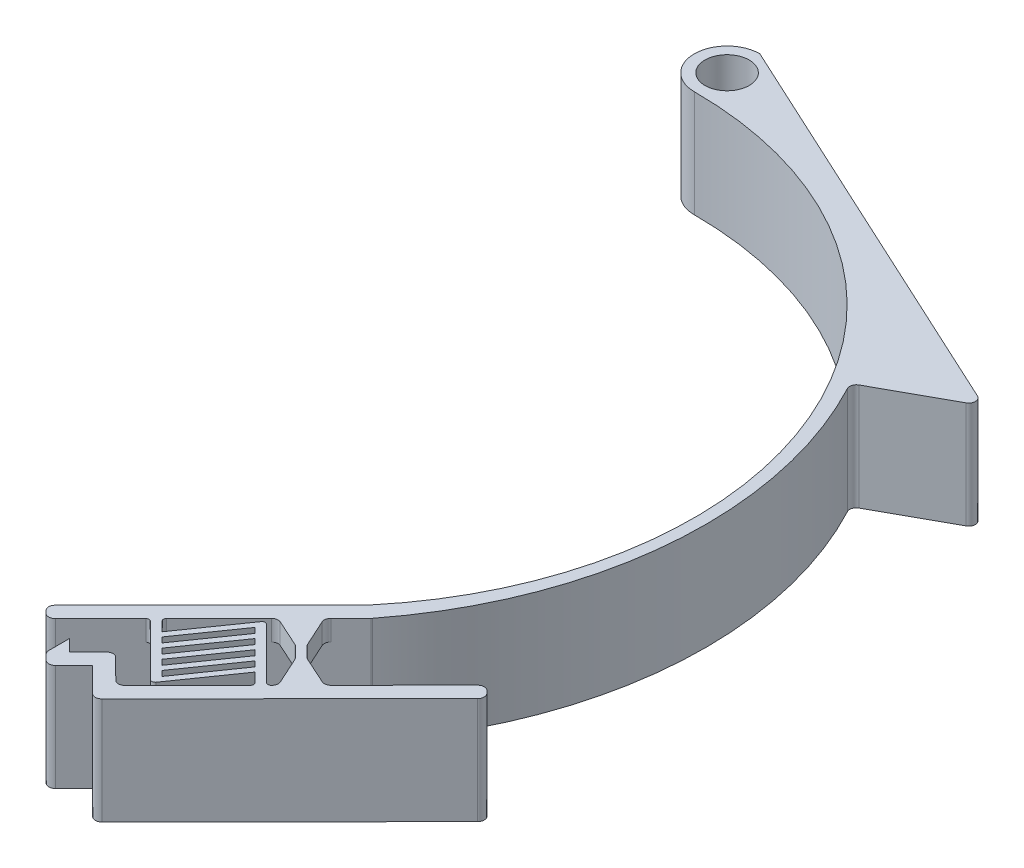
SolidWorks part; units mm, degrees
ref_plane "Front Plane" through (0, 0, 0) normal (0, 0, 1) x (1, 0, 0)
ref_plane "Top Plane" through (0, 0, 0) normal (0, 1, 0) x (1, 0, 0)
ref_plane "Right Plane" through (0, 0, 0) normal (1, 0, 0) x (0, 0, -1)
sketch "Sketch1" plane through (0, 0, 0) normal (0, 1, 0) x (1, 0, 0)
  line L0 (0, 0) -> (34.472, -28.9254) construction
  line L1 (0, 0) -> (0, -45) construction
  line L2 (0, 0) -> (63.5762, -53.3468) construction
  line L3 (0, 53) -> (50.8207, 29.4786)
  line L4 (50.8207, 29.4786) -> (40.3111, 23.6864)
  line L5 (0, 53) -> (0, 49)
  line L7 (0, 49) -> (0, 53)
  line L8 (34.472, -28.9254) -> (20.3504, -43.088)
  line L9 (20.3504, -43.088) -> (21.7666, -44.5002)
  line L10 (21.7666, -44.5002) -> (35.8883, -30.3376)
  line L11 (35.8883, -30.3376) -> (34.472, -28.9254)
  line L12 (30.2642, -52.9732) -> (28.8479, -51.561)
  line L13 (28.8479, -51.561) -> (50.0304, -30.3171)
  line L14 (50.0304, -30.3171) -> (51.4466, -31.7293)
  line L15 (51.4466, -31.7293) -> (30.2642, -52.9732)
  line L17 (22.4727, -43.7921) -> (29.2708, -50.5705)
  line L18 (36.6148, -43.7716) -> (29.8168, -36.9932)
  line L19 (29.8168, -36.9932) -> (24.5858, -44.4869)
  line L20 (24.5858, -44.4869) -> (23.1788, -43.084)
  line L21 (29.2708, -50.5705) -> (34.5017, -43.0768)
  line L22 (22.4727, -43.7921) -> (23.1788, -43.084)
  line L23 (35.9087, -44.4797) -> (34.5017, -43.0768)
  line L24 (23.1788, -43.084) -> (30.2601, -50.1448) construction
  line L25 (35.9087, -44.4797) -> (28.8274, -37.4189) construction
  line L26 (29.3086, -49.196) -> (33.9584, -42.535)
  line L27 (33.9584, -42.535) -> (33.321, -41.8995)
  line L28 (33.321, -41.8995) -> (28.6713, -48.5606)
  line L29 (28.6713, -48.5606) -> (29.3086, -49.196)
  line L30 (28.1279, -48.0187) -> (27.4906, -47.3833)
  line L31 (27.4906, -47.3833) -> (32.1403, -40.7222)
  line L32 (32.1403, -40.7222) -> (32.7777, -41.3577)
  line L33 (32.7777, -41.3577) -> (28.1279, -48.0187)
  line L34 (26.9472, -46.8415) -> (26.3099, -46.206)
  line L35 (26.3099, -46.206) -> (30.9596, -39.5449)
  line L36 (30.9596, -39.5449) -> (31.597, -40.1804)
  line L37 (31.597, -40.1804) -> (26.9472, -46.8415)
  line L38 (25.7665, -45.6642) -> (25.1292, -45.0287)
  line L39 (25.1292, -45.0287) -> (29.7789, -38.3677)
  line L40 (29.7789, -38.3677) -> (30.4163, -39.0031)
  line L41 (30.4163, -39.0031) -> (25.7665, -45.6642)
  line L42 (35.9087, -44.4797) -> (36.6148, -43.7716)
  line L43 (24.5858, -44.4869) -> (25.1292, -45.0287) construction
  line L44 (25.7665, -45.6642) -> (26.3099, -46.206) construction
  line L45 (26.9472, -46.8415) -> (27.4906, -47.3833) construction
  line L46 (28.1279, -48.0187) -> (28.6713, -48.5606) construction
  line L47 (29.3086, -49.196) -> (29.852, -49.7378) construction
  line L48 (30.2396, -36.0026) -> (34.1313, -37.7648)
  line L49 (34.1313, -37.7648) -> (35.5475, -39.1769)
  line L50 (35.5475, -39.1769) -> (37.3209, -43.0635)
  line L51 (37.3209, -43.0635) -> (40.1452, -40.2309)
  line L52 (40.1452, -40.2309) -> (36.2536, -38.4688)
  line L53 (36.2536, -38.4688) -> (34.8373, -37.0566)
  line L54 (34.8373, -37.0566) -> (33.0639, -33.1701)
  line L55 (33.0639, -33.1701) -> (30.2396, -36.0026)
  line L56 (36.0041, -30.211) -> (35.8883, -30.3376)
  line L57 (20.3504, -43.088) -> (21.7666, -44.5002)
  line L58 (20.3504, -43.088) -> (14.7017, -48.7531)
  line L59 (21.7666, -44.5002) -> (16.118, -50.1653)
  line L60 (14.7017, -48.7531) -> (16.118, -50.1653)
  line L61 (16.118, -50.1653) -> (20.3545, -45.9165) construction
  line L62 (16.118, -50.1653) -> (19.6586, -53.6957) construction
  line L63 (20.3545, -45.9165) -> (23.8951, -49.4469) construction
  line L64 (19.6586, -53.6957) -> (23.8951, -49.4469) construction
  line L69 (30.2642, -52.9732) -> (27.4399, -55.8057)
  line L70 (27.4399, -55.8057) -> (23.8992, -52.2753)
  line L71 (28.8479, -51.561) -> (30.2642, -52.9732)
  line L72 (23.8992, -52.2753) -> (21.0749, -55.1078)
  line L73 (21.0749, -55.1078) -> (19.6586, -53.6957)
  line L74 (19.6586, -53.6957) -> (23.8951, -49.4469)
  line L75 (23.8951, -49.4469) -> (27.4358, -52.9773)
  line L76 (27.4358, -52.9773) -> (28.8479, -51.561)
  line L77 (28.8479, -51.561) -> (30.2642, -52.9732)
  line L82 (19.6586, -53.6957) -> (21.0708, -52.2794)
  line L83 (21.0708, -52.2794) -> (19.6545, -50.8672)
  line L84 (19.6545, -50.8672) -> (19.6586, -53.6957)
  circle A0 centre (0, 0) radius 45 construction
  arc A1 (0, 45) -> (34.472, -28.9254) centre (0, 0) cw
  arc A2 (0, 45) -> (0, 53) centre (0, 49) cw
  arc A4 (36.0041, -30.211) -> (0, 49) centre (-2.6664, 0) ccw
  circle A5 centre (0, 49) radius 2.7
  arc A6 (40.3111, 23.6864) -> (0, 49) centre (-2.6664, 0) ccw
  dimension "D1" = 90
  dimension "D5" = 56
  dimension "D6" = 5.4
  dimension "D9" = 2
  dimension "D2" = 50
  dimension "D3" = 8
  dimension "D4" = 2
  dimension "D7" = 12
  dimension "D8" = 2
  dimension "D10" = 1
  dimension "D11" = 80
  dimension "D12" = 10
  dimension "D13" = 0.9
  dimension "D14" = 1
  dimension "D15" = 0.4
  dimension "D16" = 0.4
  dimension "D17" = 10
  dimension "D18" = 1
  dimension "D19" = 4
  dimension "D20" = 4
  dimension "D21" = 1
  dimension "D22" = 20
  dimension "D23" = 30
  dimension "D24" = 2
  dimension "D25" = 4
  dimension "D26" = 0.1716
  dimension "D27" = 4
  dimension "D28" = 8
  dimension "D29" = 5
  dimension "D30" = 2
  dimension "D31" = 2
  dimension "D32" = 2
  dimension "D33" = 2
  dimension "D34" = 2
extrude "Boss-Extrude1" add sketch "Sketch1" along normal blind 13
sketch "Sketch2" plane through (-10.6921, 0, 10.7232) normal (-0.7061, 0, 0.7081) x (0.7081, 0, 0.7061)
  line L0 (46.8344, 13) -> (46.8344, 0) construction
  line L1 (46.8344, 10.5) -> (56.8344, 10.5)
  line L2 (46.8344, 10.5) -> (46.8344, 2.5)
  line L3 (46.8344, 2.5) -> (56.8344, 2.5)
  line L4 (56.8344, 10.5) -> (56.8344, 2.5)
  line L5 (46.8344, 13) -> (56.4344, 13) construction
  dimension "D1" = 10
  dimension "D2" = 8
  dimension "D3" = 2.5
extrude "Cut-Extrude1" cut sketch "Sketch2" against normal blind 23
fillet "Fillet2" radius 0.8 25 edges at (40.3111, 6.5, -23.6864) (50.8207, 6.5, -29.4786) (37.3209, 11.75, 43.0635) (35.5475, 11.75, 39.1769) (34.1313, 11.75, 37.7648) (30.2396, 11.75, 36.0026) (33.0639, 11.75, 33.1701) (40.1452, 1.25, 40.2309) (40.1452, 11.75, 40.2309) (34.8373, 1.25, 37.0566) (36.2536, 1.25, 38.4688) (34.8373, 11.75, 37.0566) (36.2536, 11.75, 38.4688) (50.0304, 6.5, 30.3171) (51.4466, 6.5, 31.7293) (27.4399, 6.5, 55.8057) (27.4358, 6.5, 52.9773) (23.8951, 6.5, 49.4469) (19.6586, 6.5, 53.6957) (21.0749, 6.5, 55.1078) (16.118, 6.5, 50.1653) (14.7017, 6.5, 48.7531) (30.2396, 1.25, 36.0026) (33.0639, 1.25, 33.1701) (37.3209, 1.25, 43.0635)
fillet "Fillet3" radius 0.4 12 edges at (23.1788, 1.25, 43.084) (22.4727, 1.25, 43.7921) (35.9087, 1.25, 44.4797) (29.2708, 1.25, 50.5705) (36.6148, 1.25, 43.7716) (29.8168, 1.25, 36.9932) (29.8168, 11.75, 36.9932) (23.1788, 11.75, 43.084) (22.4727, 11.75, 43.7921) (29.2708, 11.75, 50.5705) (36.6148, 11.75, 43.7716) (35.9087, 11.75, 44.4797)
